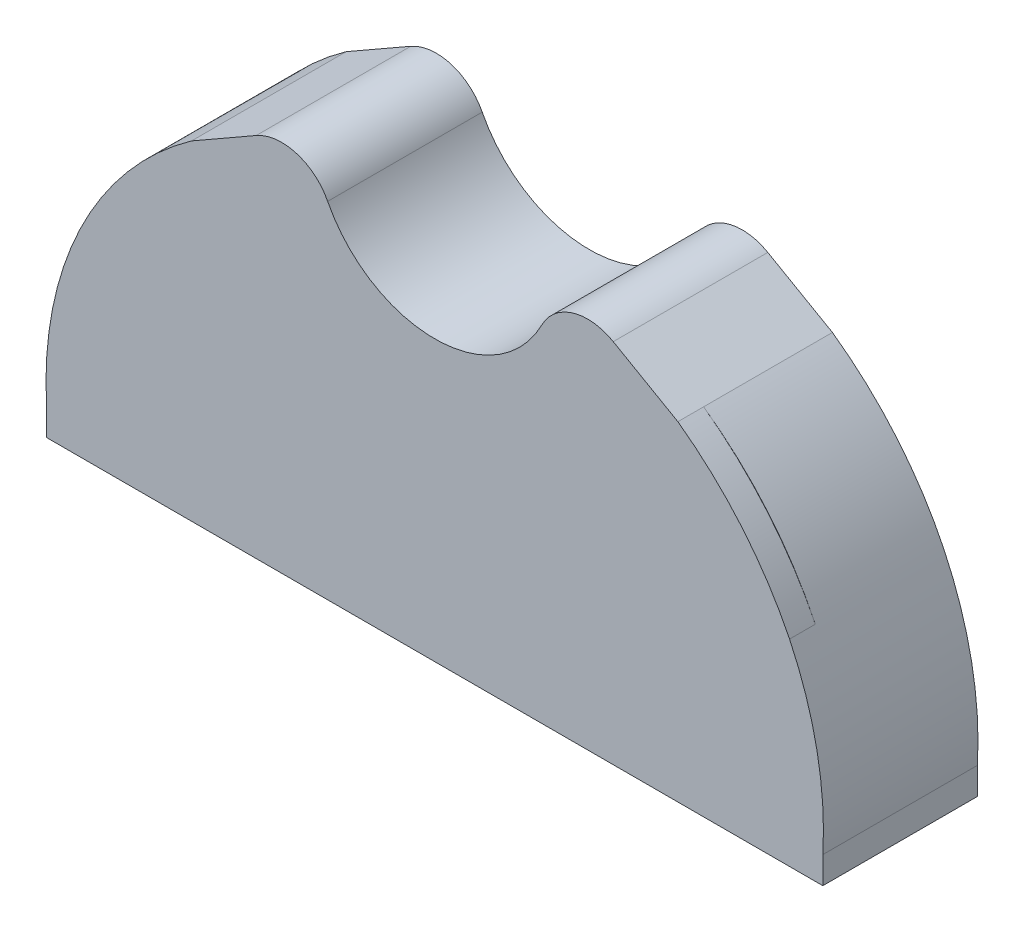
SolidWorks part; units mm, degrees
ref_plane "Front Plane" through (0, 0, 0) normal (0, 0, 1) x (1, 0, 0)
ref_plane "Top Plane" through (0, 0, 0) normal (0, 1, 0) x (1, 0, 0)
ref_plane "Right Plane" through (0, 0, 0) normal (1, 0, 0) x (0, 0, -1)
sketch "Sketch1" plane through (0, 0, 0) normal (0, 0, 1) x (1, 0, 0)
  line L0 (27.7778, 5.0997) -> (27.8278, 5.0997) construction
  line L5 (7.7778, -14.9003) -> (7.7778, 5.0997) construction
  line L7 (7.7278, 5.0997) -> (7.7278, 4.3155)
  line L9 (27.8278, 5.0997) -> (27.8278, 4.3155)
  line L10 (27.7778, 5.0997) -> (27.7778, -14.9003) construction
  line L11 (11.5127, 12.8939) -> (11.4814, 12.9328) construction
  line L12 (14.5883, 12.1586) -> (14.6339, 12.1792) construction
  line L13 (20.9674, 12.1586) -> (20.9218, 12.1792) construction
  line L14 (24.043, 12.8939) -> (24.0743, 12.9328) construction
  line L15 (11.5127, 12.8939) -> (12.1392, 12.1144) construction
  line L16 (14.5883, 12.1586) -> (13.677, 11.7468) construction
  line L17 (7.7278, 4.3155) -> (27.8278, 4.3155)
  line L18 (20.9674, 12.1586) -> (21.8787, 11.7468) construction
  line L19 (24.043, 12.8939) -> (23.4165, 12.1144) construction
  line L20 (7.7278, 4.3155) -> (6.4778, 4.3155)
  line L21 (7.7278, 5.0997) -> (6.4778, 5.0997)
  line L22 (11.4814, 12.9328) -> (10.6983, 13.9071)
  line L23 (14.6339, 12.1792) -> (15.773, 12.6939)
  line L24 (6.4778, 4.3155) -> (6.4778, 5.0997)
  line L25 (20.9218, 12.1792) -> (19.7827, 12.6939)
  line L26 (24.0743, 12.9328) -> (24.8574, 13.9071)
  line L27 (27.8278, 5.0997) -> (29.0778, 5.0997)
  line L28 (27.8278, 4.3155) -> (29.0778, 4.3155)
  line L29 (17.7778, 10.0997) -> (17.7778, 15.4172) construction
  line L30 (13.4503, 15.9557) -> (23.0806, 15.9557) construction
  line L31 (14.2778, 15.9557) -> (10.6983, 13.9071)
  line L32 (21.2778, 15.9557) -> (24.8574, 13.9071)
  line L35 (29.0778, 4.3155) -> (29.0778, 5.0997)
  arc A0 (7.7278, 5.0997) -> (11.4814, 12.9328) centre (17.7778, 5.0997) cw
  arc A1 (11.5127, 12.8939) -> (7.7778, 5.0997) centre (17.7778, 5.0997) ccw construction
  arc A2 (11.4814, 12.9328) -> (14.6339, 12.1792) centre (12.7658, 11.335) cw
  arc A3 (14.5883, 12.1586) -> (11.5127, 12.8939) centre (12.7658, 11.335) ccw construction
  arc A4 (14.6339, 12.1792) -> (20.9218, 12.1792) centre (17.7778, 13.5997) ccw
  arc A5 (14.5883, 12.1586) -> (20.9674, 12.1586) centre (17.7778, 13.5997) ccw construction
  arc A6 (20.9218, 12.1792) -> (24.0743, 12.9328) centre (22.7899, 11.335) cw
  arc A7 (10.6983, 13.9071) -> (6.4778, 5.0997) centre (16.5095, 5.7075) ccw
  arc A8 (14.2778, 15.9557) -> (21.2778, 15.9557) centre (17.7778, 15.9557) ccw
  arc A11 (29.0778, 5.0997) -> (24.8574, 13.9071) centre (19.0462, 5.7075) ccw
  arc A12 (24.0743, 12.9328) -> (27.8278, 5.0997) centre (17.7778, 5.0997) cw
  circle A13 centre (17.7778, 15.9557) radius 3.5 construction
  dimension "D5" = 7
  dimension "D1" = 0.05
  dimension "D2" = 0.05
  dimension "D3" = 0.05
  dimension "D4" = 0.05
  dimension "D6" = 1.25
extrude "Boss-Extrude1" add sketch "Sketch1" against normal up to surface (2.8349 mm away) and the other way up to surface (0.9151 mm away)
fillet "Fillet1" radius 1.5 2 edges at (14.2778, 15.9557, -0.9599) (21.2778, 15.9557, -0.9599)
sketch "Sketch3" plane through (0, 0, 0.9151) normal (0, 0, 1) x (1, 0, 0)
  line L0 (6.4778, 5.0997) -> (6.4778, 4.3155) construction
  line L1 (10.6983, 13.9071) -> (12.5797, 14.9838)
  line L2 (22.976, 14.9838) -> (24.8574, 13.9071)
  line L3 (29.0778, 5.0997) -> (29.0778, 4.3155)
  line L4 (6.4778, 4.7076) -> (6.4778, 4.3155)
  line L5 (6.4778, 4.3155) -> (7.7278, 4.3155)
  line L7 (7.7278, 4.3155) -> (27.8278, 4.3155)
  line L8 (27.8278, 4.3155) -> (29.0778, 4.3155)
  line L17 (12.5797, 14.9838) -> (10.6983, 13.9071)
  line L18 (6.4778, 5.0997) -> (6.4778, 4.3155)
  line L19 (6.4778, 4.3155) -> (7.7278, 4.3155)
  line L20 (7.7278, 4.3155) -> (7.7278, 5.0997)
  line L21 (27.8278, 5.0997) -> (27.8278, 4.3155)
  line L22 (27.8278, 4.3155) -> (29.0778, 4.3155)
  line L23 (29.0778, 4.3155) -> (29.0778, 5.0997)
  line L24 (24.8574, 13.9071) -> (22.976, 14.9838)
  line L25 (12.5797, 14.9838) -> (10.6983, 13.9071)
  line L26 (6.4778, 5.0997) -> (6.4778, 4.3155)
  line L27 (6.4778, 4.3155) -> (7.7278, 4.3155)
  line L30 (27.8278, 4.3155) -> (29.0778, 4.3155)
  line L31 (29.0778, 4.3155) -> (29.0778, 5.0997)
  line L32 (24.8574, 13.9071) -> (22.976, 14.9838)
  arc A0 (6.4778, 4.7076) -> (7.4463, 10.0505) centre (16.7075, 5.6126) cw
  arc A1 (10.6983, 13.9071) -> (6.4778, 5.0997) centre (16.5095, 5.7075) ccw construction
  arc A2 (12.5797, 14.9838) -> (14.6607, 14.3641) centre (13.3247, 13.6819) cw
  arc A3 (14.6607, 14.3641) -> (20.895, 14.3641) centre (17.7778, 15.9557) ccw
  arc A4 (20.895, 14.3641) -> (22.976, 14.9838) centre (22.231, 13.6819) cw
  arc A5 (24.8574, 13.9071) -> (28.1094, 10.0505) centre (18.7505, 5.4582) cw
  arc A6 (29.0778, 5.0997) -> (24.8574, 13.9071) centre (19.0462, 5.7075) ccw construction
  arc A7 (28.1094, 10.0505) -> (29.0778, 5.0997) centre (19.3996, 5.7767) cw
  arc A23 (14.6607, 14.3641) -> (20.895, 14.3641) centre (17.7778, 15.9557) ccw
  arc A24 (14.6607, 14.3641) -> (12.5797, 14.9838) centre (13.3247, 13.6819) ccw
  arc A25 (10.6983, 13.9071) -> (6.4778, 5.0997) centre (16.5095, 5.7075) ccw
  arc A26 (11.4814, 12.9328) -> (7.7278, 5.0997) centre (17.7778, 5.0997) ccw
  arc A27 (14.6339, 12.1792) -> (11.4814, 12.9328) centre (12.7658, 11.335) ccw
  arc A28 (14.6339, 12.1792) -> (20.9218, 12.1792) centre (17.7778, 13.5997) ccw
  arc A29 (24.0743, 12.9328) -> (20.9218, 12.1792) centre (22.7899, 11.335) ccw
  arc A30 (27.8278, 5.0997) -> (24.0743, 12.9328) centre (17.7778, 5.0997) ccw
  arc A31 (29.0778, 5.0997) -> (24.8574, 13.9071) centre (19.0462, 5.7075) ccw
  arc A32 (22.976, 14.9838) -> (20.895, 14.3641) centre (22.231, 13.6819) ccw
  arc A33 (14.6607, 14.3641) -> (20.895, 14.3641) centre (17.7778, 15.9557) ccw
  arc A34 (14.6607, 14.3641) -> (12.5797, 14.9838) centre (13.3247, 13.6819) ccw
  arc A35 (7.4463, 10.0505) -> (6.4778, 5.0997) centre (16.5095, 5.7075) ccw
  arc A41 (29.0778, 5.0997) -> (24.8574, 13.9071) centre (19.0462, 5.7075) ccw
  arc A42 (22.976, 14.9838) -> (20.895, 14.3641) centre (22.231, 13.6819) ccw
  arc M20 (20.895, 14.3641) -> (14.6607, 14.3641) centre (17.7778, 15.9557) cw
  arc M21 (14.6607, 14.3641) -> (12.5797, 14.9838) centre (13.3247, 13.6819) ccw
  line M22 (12.5797, 14.9838) -> (10.6983, 13.9071)
  arc M23 (10.6983, 13.9071) -> (6.4778, 5.0997) centre (16.5095, 5.7075) ccw
  line M24 (6.4778, 5.0997) -> (6.4778, 4.3155)
  line M25 (6.4778, 4.3155) -> (7.7278, 4.3155)
  line M26 (7.7278, 4.3155) -> (7.7278, 5.0997)
  arc M27 (7.7278, 5.0997) -> (11.4814, 12.9328) centre (17.7778, 5.0997) cw
  arc M28 (11.4814, 12.9328) -> (14.6339, 12.1792) centre (12.7658, 11.335) cw
  arc M29 (14.6339, 12.1792) -> (20.9218, 12.1792) centre (17.7778, 13.5997) ccw
  arc M30 (20.9218, 12.1792) -> (24.0743, 12.9328) centre (22.7899, 11.335) cw
  arc M31 (24.0743, 12.9328) -> (27.8278, 5.0997) centre (17.7778, 5.0997) cw
  line M32 (27.8278, 5.0997) -> (27.8278, 4.3155)
  line M33 (27.8278, 4.3155) -> (29.0778, 4.3155)
  line M34 (29.0778, 4.3155) -> (29.0778, 5.0997)
  arc M35 (29.0778, 5.0997) -> (24.8574, 13.9071) centre (19.0462, 5.7075) ccw
  line M36 (24.8574, 13.9071) -> (22.976, 14.9838)
  arc M37 (22.976, 14.9838) -> (20.895, 14.3641) centre (22.231, 13.6819) ccw
  dimension "D1" = 0
extrude "Boss-Extrude2" add sketch "Sketch3" along normal blind 0.75 contours L7 M26 M32 M31 M30 M29 M28 M27 | M37 M20 M21 M22 M23 M24 M25 M26 M27 M28 M29 M30 M31 M32 M33 M34 M35 M36
